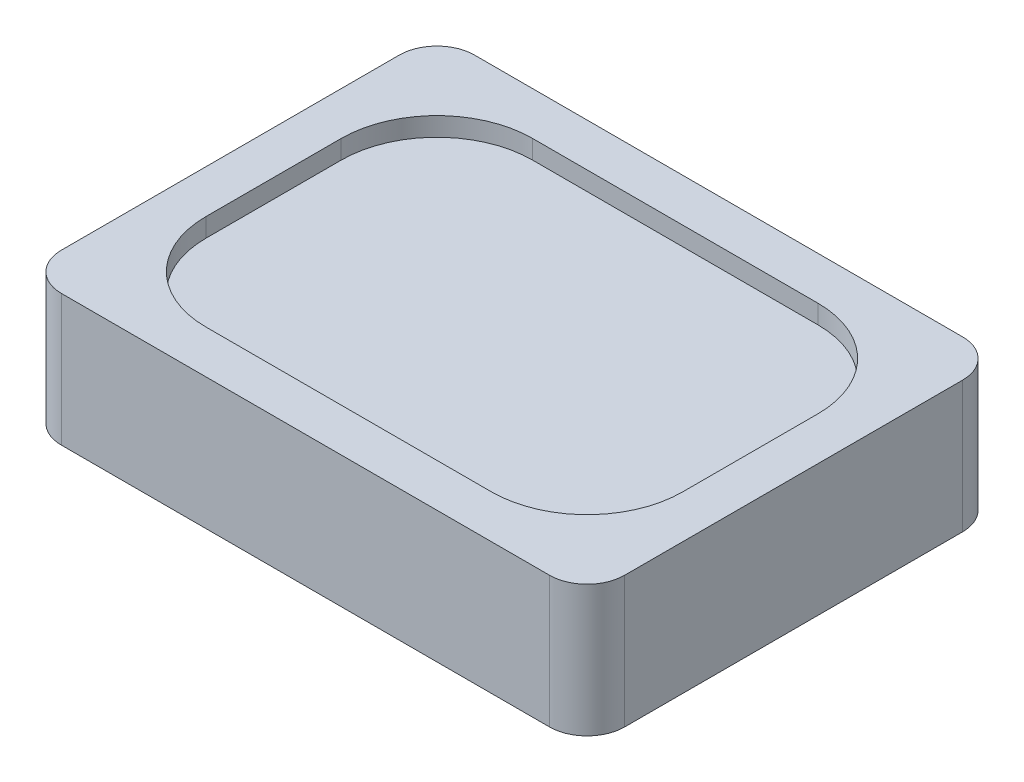
SolidWorks part; units mm, degrees
ref_plane "Front Plane" through (0, 0, 0) normal (0, 0, 1) x (1, 0, 0)
ref_plane "Top Plane" through (0, 0, 0) normal (0, 1, 0) x (1, 0, 0)
ref_plane "Right Plane" through (0, 0, 0) normal (1, 0, 0) x (0, 0, -1)
sketch "Sketch1" plane through (0, 0, 0) normal (0, 1, 0) x (1, 0, 0)
  line L1 (-7.5, -5.5) -> (7.5, -5.5)
  line L2 (-7.5, -5.5) -> (-7.5, 5.5)
  line L3 (-7.5, 5.5) -> (7.5, 5.5)
  line L4 (7.5, -5.5) -> (7.5, 5.5)
  line L5 (-7.5, -5.5) -> (7.5, 5.5) construction
  line L6 (-7.5, 5.5) -> (7.5, -5.5) construction
  point P0 (0, 0)
  dimension "D1" = 11
  dimension "D2" = 15
extrude "Boss-Extrude1" add sketch "Sketch1" along normal blind 3.5
fillet "Fillet1" radius 1 4 edges at (-7.5, 1.75, -5.5) (7.5, 1.75, -5.5) (7.5, 1.75, 5.5) (-7.5, 1.75, 5.5)
sketch "Sketch2" plane through (0, 3.5, 0) normal (0, 1, 0) x (1, 0, 0)
  line L1 (-6.35, -4.35) -> (6.35, -4.35)
  line L2 (-6.35, -4.35) -> (-6.35, 4.35)
  line L3 (-6.35, 4.35) -> (6.35, 4.35)
  line L4 (6.35, -4.35) -> (6.35, 4.35)
  line L5 (-6.35, -4.35) -> (6.35, 4.35) construction
  line L6 (-6.35, 4.35) -> (6.35, -4.35) construction
  point P0 (0, 0)
  dimension "D1" = 12.7
  dimension "D2" = 8.7
extrude "Cut-Extrude1" cut sketch "Sketch2" against normal blind 0.5
fillet "Fillet2" radius 2.55 4 edges at (6.35, 3.25, 4.35) (-6.35, 3.25, 4.35) (-6.35, 3.25, -4.35) (6.35, 3.25, -4.35)
